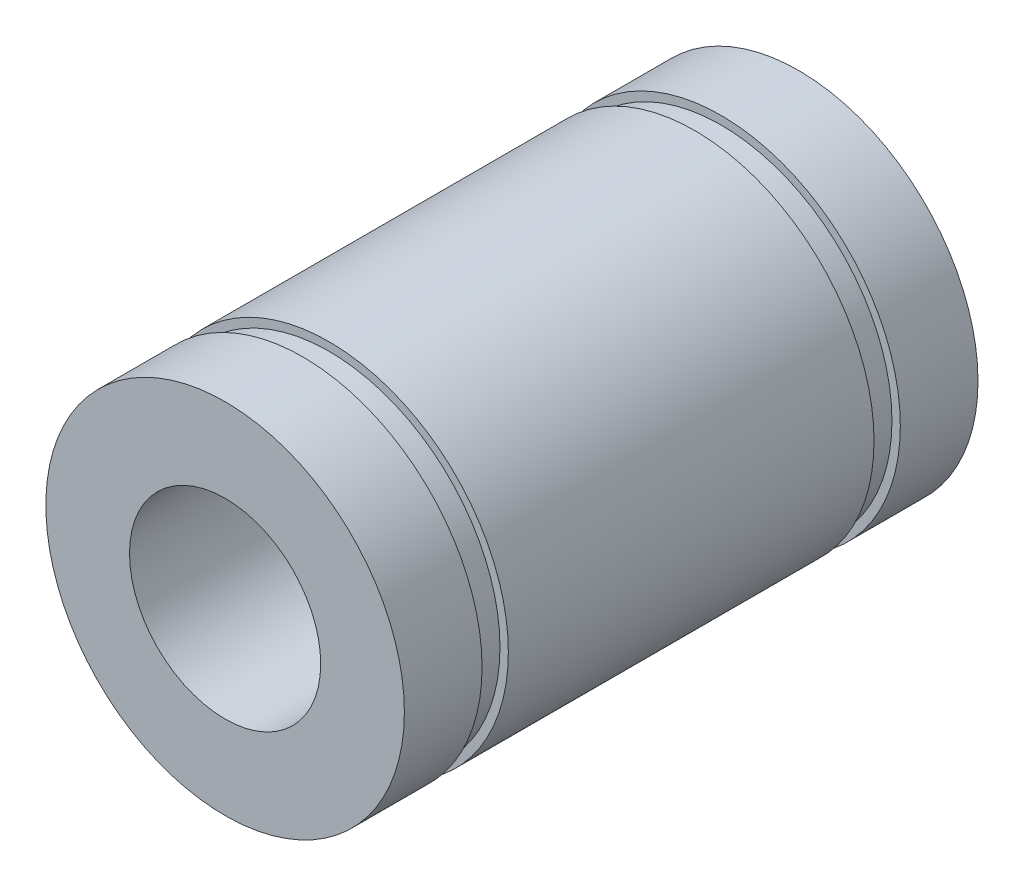
SolidWorks part; units mm, degrees
ref_plane "Front Plane" through (0, 0, 0) normal (0, 0, 1) x (1, 0, 0)
ref_plane "Top Plane" through (0, 0, 0) normal (0, 1, 0) x (1, 0, 0)
ref_plane "Right Plane" through (0, 0, 0) normal (1, 0, 0) x (0, 0, -1)
sketch "Sketch1" plane through (0, 0, 0) normal (0, 1, 0) x (1, 0, 0)
  line L0 (7.5, 0) -> (4, 0)
  line L1 (4, 0) -> (4, -24)
  line L2 (4, -24) -> (7.5, -24)
  line L3 (7.5, -24) -> (7.5, -20.75)
  line L4 (7.5, -20.75) -> (7.15, -20.75)
  line L5 (7.15, -20.75) -> (7.15, -19.65)
  line L6 (7.15, -19.65) -> (7.5, -19.65)
  line L7 (7.5, -19.65) -> (7.5, -4.35)
  line L8 (7.5, -4.35) -> (7.15, -4.35)
  line L9 (7.15, -4.35) -> (7.15, -3.25)
  line L10 (7.15, -3.25) -> (7.5, -3.25)
  line L11 (7.5, -3.25) -> (7.5, 0)
  line L12 (0, 0) -> (0, -24) construction
revolve "Revolve1" add sketch "Sketch1" angle 360 about L12
